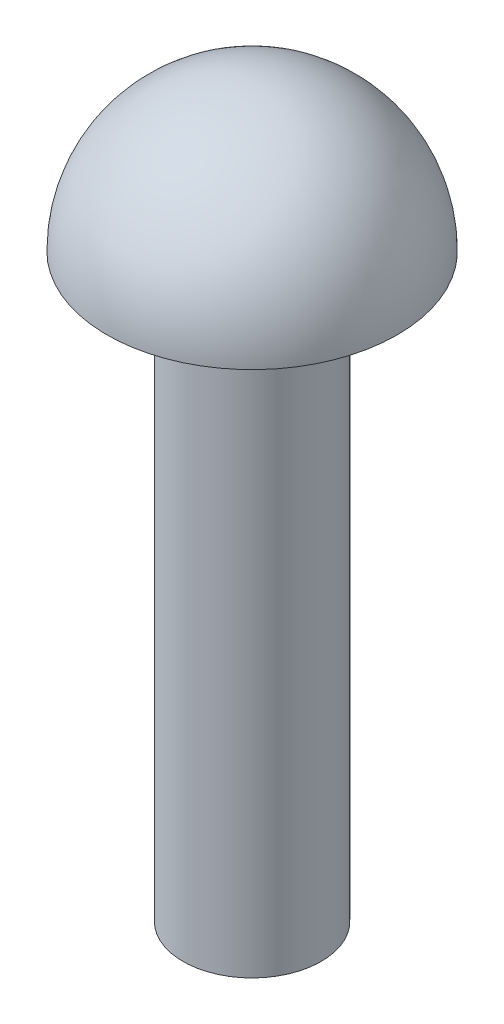
SolidWorks part; units mm, degrees
ref_plane "Alzado" through (0, 0, 0) normal (0, 0, 1) x (1, 0, 0)
ref_plane "Planta" through (0, 0, 0) normal (0, 1, 0) x (1, 0, 0)
ref_plane "Vista lateral" through (0, 0, 0) normal (1, 0, 0) x (0, 0, -1)
sketch "Croquis1" plane through (0, 0, 0) normal (0, 0, 1) x (1, 0, 0)
  line L0 (0, 0) -> (0, 50) construction
  line L1 (0, 0) -> (4.7625, 0)
  line L2 (4.7625, 0) -> (4.7625, 40)
  line L3 (4.7625, 40) -> (10, 40)
  line L4 (0, 0) -> (0, 50)
  arc A0 (10, 40) -> (0, 50) centre (0, 40) ccw
  dimension "D1" = 9.525
  dimension "D2" = 40
  dimension "D3" = 10
revolve "Revolución1" add sketch "Croquis1" angle 360 about L0
